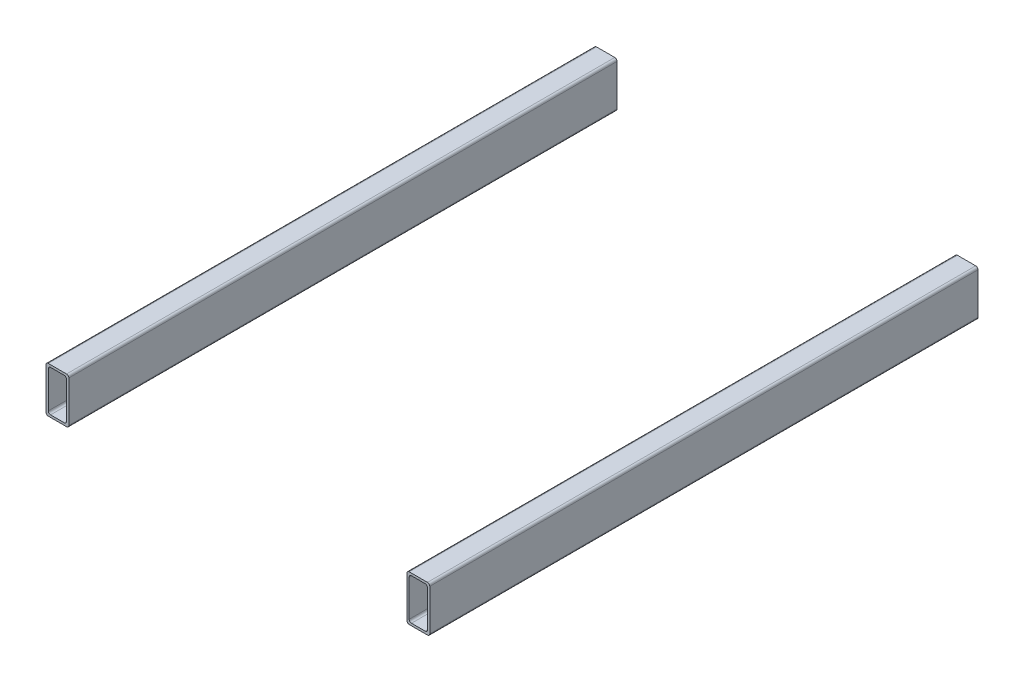
SolidWorks part; units mm, degrees
ref_plane "Спереди" through (0, 0, 0) normal (0, 0, 1) x (1, 0, 0)
ref_plane "Сверху" through (0, 0, 0) normal (0, 1, 0) x (1, 0, 0)
ref_plane "Справа" through (0, 0, 0) normal (1, 0, 0) x (0, 0, -1)
sketch "Эскиз1" plane through (0, 0, 0) normal (0, 0, 1) x (1, 0, 0)
  line L16 (-10, 50) -> (10, 50)
  line L17 (12.5, 47.5) -> (12.5, 2.5)
  line L18 (10, 0) -> (-10, 0)
  line L19 (-12.5, 2.5) -> (-12.5, 47.5)
  line L20 (-7.5, 47.5) -> (7.5, 47.5)
  line L21 (10, 45) -> (10, 5)
  line L22 (7.5, 2.5) -> (-7.5, 2.5)
  line L23 (-10, 5) -> (-10, 45)
  line L24 (385, 50) -> (405, 50)
  line L25 (407.5, 47.5) -> (407.5, 2.5)
  line L26 (405, 0) -> (385, 0)
  line L27 (382.5, 2.5) -> (382.5, 47.5)
  line L28 (387.5, 47.5) -> (402.5, 47.5)
  line L29 (405, 45) -> (405, 5)
  line L30 (402.5, 2.5) -> (387.5, 2.5)
  line L31 (385, 5) -> (385, 45)
  arc A16 (12.5, 47.5) -> (10, 50) centre (10, 47.5) ccw
  arc A17 (10, 0) -> (12.5, 2.5) centre (10, 2.5) ccw
  arc A18 (-12.5, 2.5) -> (-10, 0) centre (-10, 2.5) ccw
  arc A19 (-10, 50) -> (-12.5, 47.5) centre (-10, 47.5) ccw
  arc A20 (10, 45) -> (7.5, 47.5) centre (7.5, 45) ccw
  arc A21 (7.5, 2.5) -> (10, 5) centre (7.5, 5) ccw
  arc A22 (-10, 5) -> (-7.5, 2.5) centre (-7.5, 5) ccw
  arc A23 (-7.5, 47.5) -> (-10, 45) centre (-7.5, 45) ccw
  arc A24 (407.5, 47.5) -> (405, 50) centre (405, 47.5) ccw
  arc A25 (405, 0) -> (407.5, 2.5) centre (405, 2.5) ccw
  arc A26 (382.5, 2.5) -> (385, 0) centre (385, 2.5) ccw
  arc A27 (385, 50) -> (382.5, 47.5) centre (385, 47.5) ccw
  arc A28 (405, 45) -> (402.5, 47.5) centre (402.5, 45) ccw
  arc A29 (402.5, 2.5) -> (405, 5) centre (402.5, 5) ccw
  arc A30 (385, 5) -> (387.5, 2.5) centre (387.5, 5) ccw
  arc A31 (387.5, 47.5) -> (385, 45) centre (387.5, 45) ccw
extrude "Бобышка-Вытянуть1" add sketch "Эскиз1" against normal blind 600
